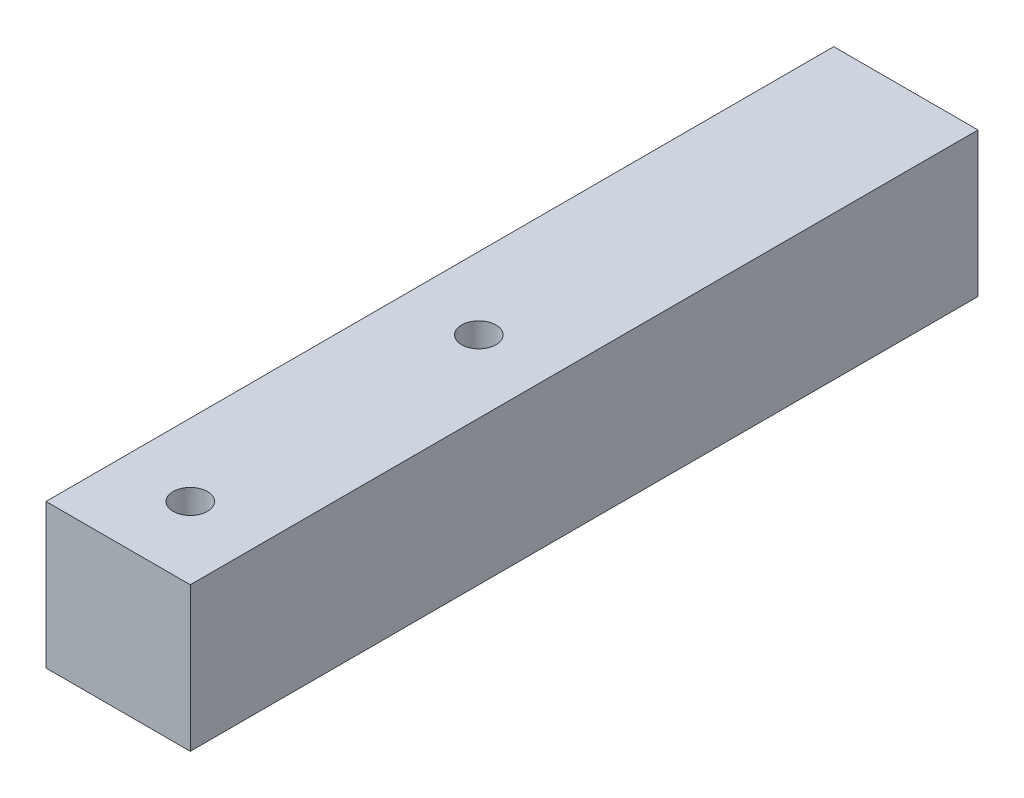
SolidWorks part; units mm, degrees
ref_plane "Front Plane" through (0, 0, 0) normal (0, 0, 1) x (1, 0, 0)
ref_plane "Top Plane" through (0, 0, 0) normal (0, 1, 0) x (1, 0, 0)
ref_plane "Right Plane" through (0, 0, 0) normal (1, 0, 0) x (0, 0, -1)
sketch "Sketch1" plane through (0, 0, 0) normal (0, 0, 1) x (1, 0, 0)
  line L1 (-12.7, -12.7) -> (12.7, -12.7)
  line L2 (-12.7, -12.7) -> (-12.7, 12.7)
  line L3 (-12.7, 12.7) -> (12.7, 12.7)
  line L4 (12.7, -12.7) -> (12.7, 12.7)
  line L5 (-12.7, -12.7) -> (12.7, 12.7) construction
  line L6 (-12.7, 12.7) -> (12.7, -12.7) construction
  point P0 (0, 0)
  dimension "D1" = 25.4
  dimension "D2" = 25.4
extrude "Boss-Extrude1" add sketch "Sketch1" along normal mid plane 138.683
hole_wizard "Ø6.05 (6.05) Diameter Hole1" positions "Sketch3" profile "Sketch2" hole size "Ø6.05" standard "Lanco STD" end condition through all
sketch "Sketch3" plane through (0, -12.7, 0) normal (0, -1, 0) x (-1, 0, 0)
  line L0 (12.7, -69.3415) -> (-12.7, -69.3415) construction
  point P0 (0, -5.8415)
  point P2 (0, -56.6415)
  point P5 (0, -69.3415)
  dimension "D1" = 63.5
  dimension "D2" = 12.7
sketch "Sketch2" plane through (0, -12.7, 5.8415) normal (1, 0, 0) x (0, 0, -1)
  line L0 (0, 0) -> (0, 25.4)
  line L1 (0, 25.4) -> (3.025, 25.4)
  line L2 (3.025, 25.4) -> (3.025, 0)
  line L5 (3.025, 0) -> (0, 0)
  line L11 (0, -6.35) -> (0, 107.95) construction
  dimension "Thru Hole Dia." = 6.05
  dimension "Thru Hole Depth" = 25.4
hole_wizard "Tap Drill for M6x0.75 Tap1" positions "Sketch6" profile "Sketch5" hole size "M6x0.75" standard "Lanco STD"
sketch "Sketch6" plane through (0, 0, -69.3415) normal (0, 0, -1) x (-1, 0, 0)
  point P0 (0, 0)
sketch "Sketch5" plane through (0, 0, -69.3415) normal (1, 0, 0) x (0, 1, 0)
  line L0 (0, 0) -> (0, 14.732)
  line L1 (0, 14.732) -> (2.625, 14.732)
  line L2 (2.625, 14.732) -> (2.625, 0)
  line L5 (2.625, 0) -> (0, 0)
  line L10 (0, 14.732) -> (-2.625, 14.732) construction
  line L11 (0, -6.35) -> (0, 107.95) construction
  dimension "Hole Dia." = 5.25
  dimension "Hole Depth" = 14.732
  dimension "Drill Angle" = 180
